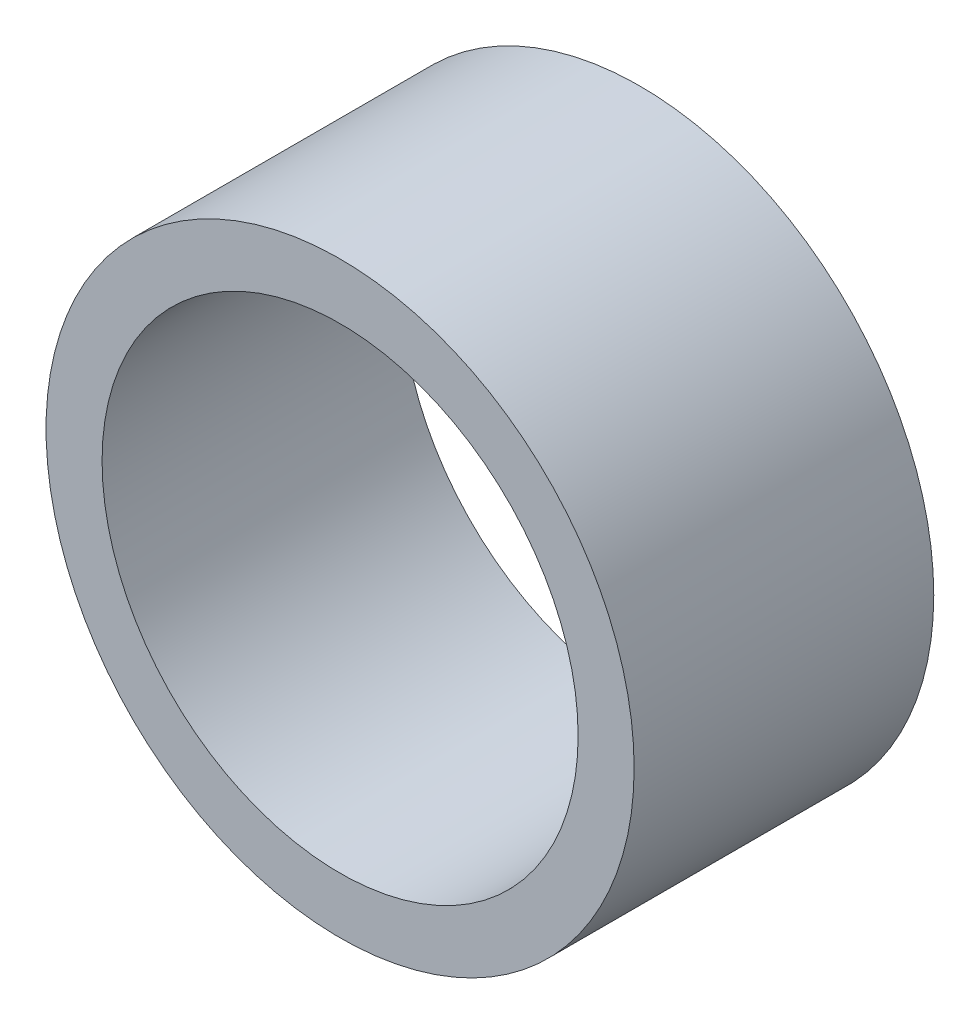
SolidWorks part; units mm, degrees
ref_plane "Ebene vorne" through (0, 0, 0) normal (0, 0, 1) x (1, 0, 0)
ref_plane "Ebene oben" through (0, 0, 0) normal (0, 1, 0) x (1, 0, 0)
ref_plane "Ebene rechts" through (0, 0, 0) normal (1, 0, 0) x (0, 0, -1)
sketch "Skizze1" plane through (0, 0, 0) normal (0, 0, 1) x (1, 0, 0)
  circle A0 centre (0, 0) radius 8.5
  circle A1 centre (0, 0) radius 10.5
  dimension "D1" = 17
  dimension "D2" = 21
extrude "Aufsatz-Linear austragen1" add sketch "Skizze1" along normal blind 10.7
